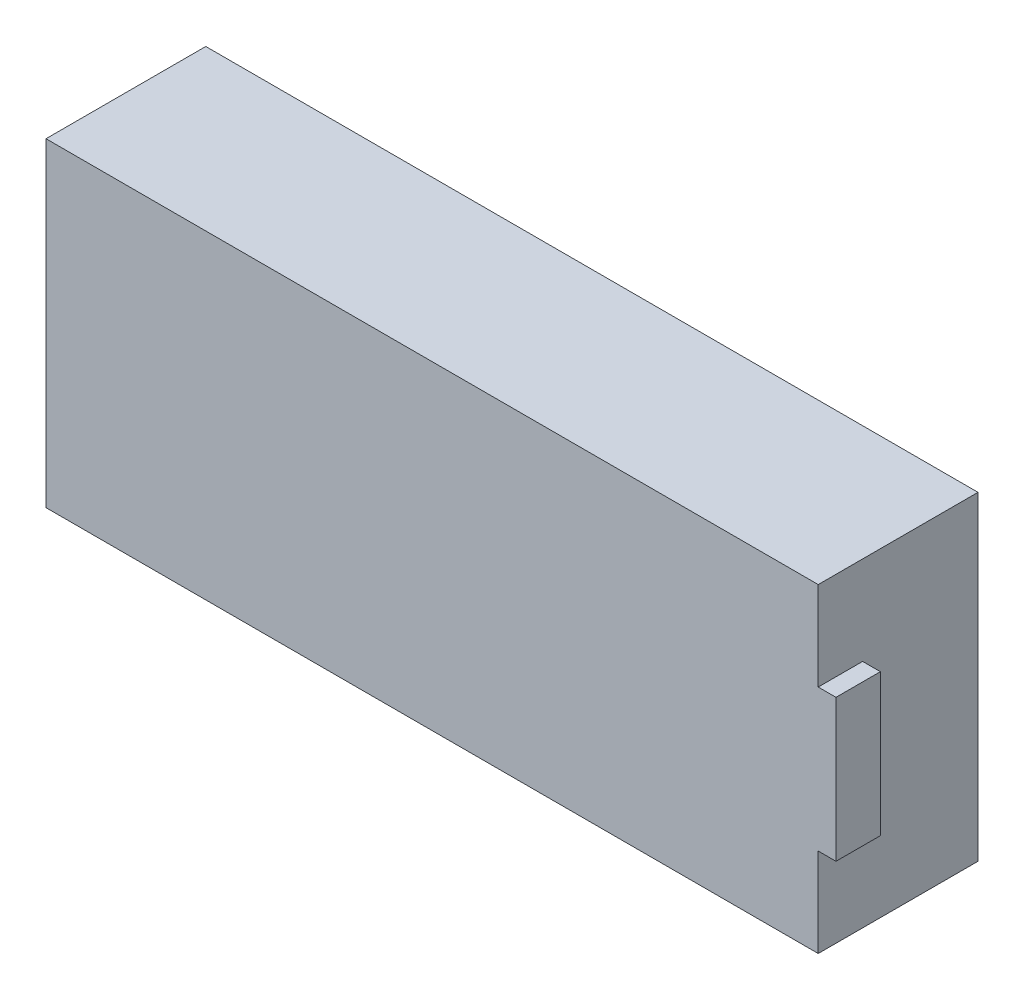
SolidWorks part; units mm, degrees
ref_plane "Front Plane" through (0, 0, 0) normal (0, 0, 1) x (1, 0, 0)
ref_plane "Top Plane" through (0, 0, 0) normal (0, 1, 0) x (1, 0, 0)
ref_plane "Right Plane" through (0, 0, 0) normal (1, 0, 0) x (0, 0, -1)
sketch "Sketch1" plane through (0, 0, 0) normal (0, 0, 1) x (1, 0, 0)
  line L1 (0, 0) -> (43.5, 0)
  line L2 (0, 0) -> (0, 18)
  line L3 (0, 18) -> (43.5, 18)
  line L4 (43.5, 0) -> (43.5, 18)
  dimension "D1" = 43.5
  dimension "D2" = 18
extrude "Boss-Extrude1" add sketch "Sketch1" along normal blind 9
sketch "Sketch2" plane through (43.5, 0, 0) normal (1, 0, 0) x (0, 0, -1)
  line L0 (-9, 0) -> (-9, 18) construction
  line L1 (-6.5, 13) -> (-9, 13)
  line L2 (-6.5, 13) -> (-6.5, 5)
  line L3 (-6.5, 5) -> (-9, 5)
  line L4 (-9, 13) -> (-9, 5)
  point P6 (-9, 9)
  dimension "D1" = 8
  dimension "D2" = 2.5
extrude "Boss-Extrude2" add sketch "Sketch2" along normal blind 1
